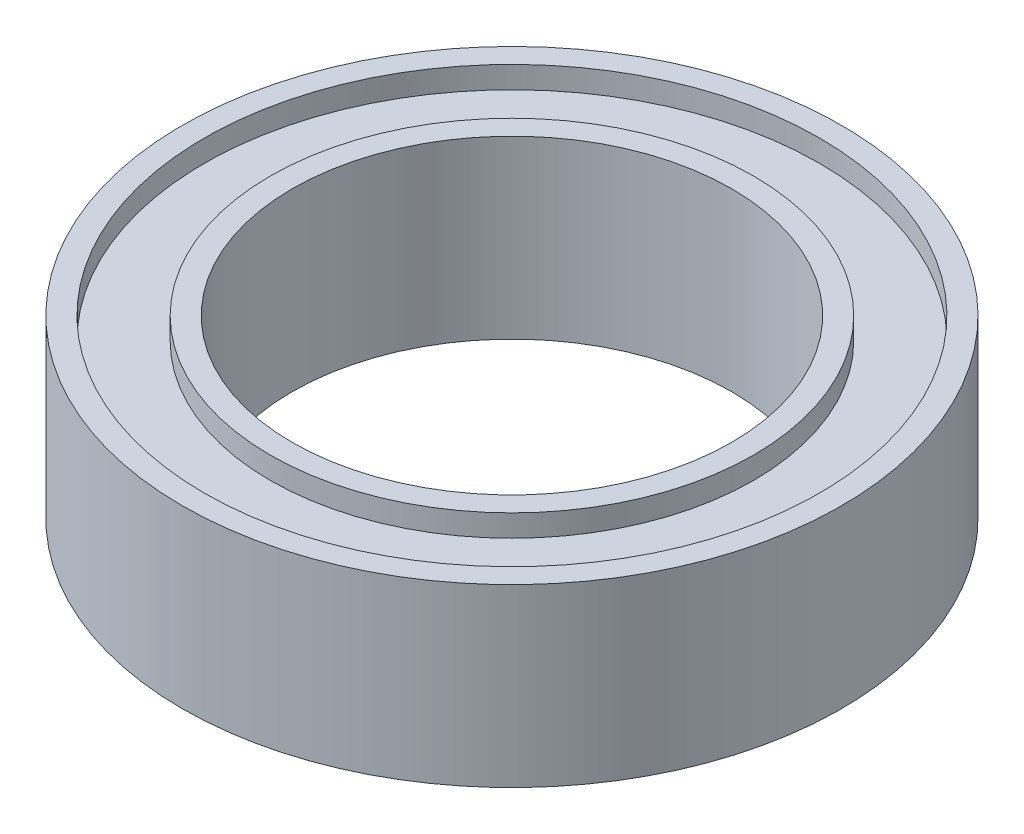
SolidWorks part; units mm, degrees
ref_plane "Front Plane" through (0, 0, 0) normal (0, 0, 1) x (1, 0, 0)
ref_plane "Top Plane" through (0, 0, 0) normal (0, 1, 0) x (1, 0, 0)
ref_plane "Right Plane" through (0, 0, 0) normal (1, 0, 0) x (0, 0, -1)
sketch "Sketch1" plane through (0, 0, 0) normal (0, 1, 0) x (1, 0, 0)
  circle A0 centre (0, 0) radius 5
  circle A1 centre (0, 0) radius 7.5
  dimension "D1" = 15
  dimension "D2" = 10
extrude "Boss-Extrude1" add sketch "Sketch1" along normal blind 4
sketch "Sketch2" plane through (0, 4, 0) normal (0, 1, 0) x (1, 0, 0)
  circle A5 centre (0, 0) radius 7
  circle A6 centre (0, 0) radius 7
  circle A8 centre (0, 0) radius 5.5
  circle A9 centre (0, 0) radius 5.5
  dimension "D1" = 0.5
  dimension "D2" = 0.5
extrude "Cut-Extrude1" cut sketch "Sketch2" against normal blind 0.5
ref_plane "Plane1" through (0, 2, 0) normal (0, -1, 0) x (-1, 0, 0)
mirror "Mirror1" about plane through (0, 2, 0) normal (0, -1, 0) of "Cut-Extrude1"
